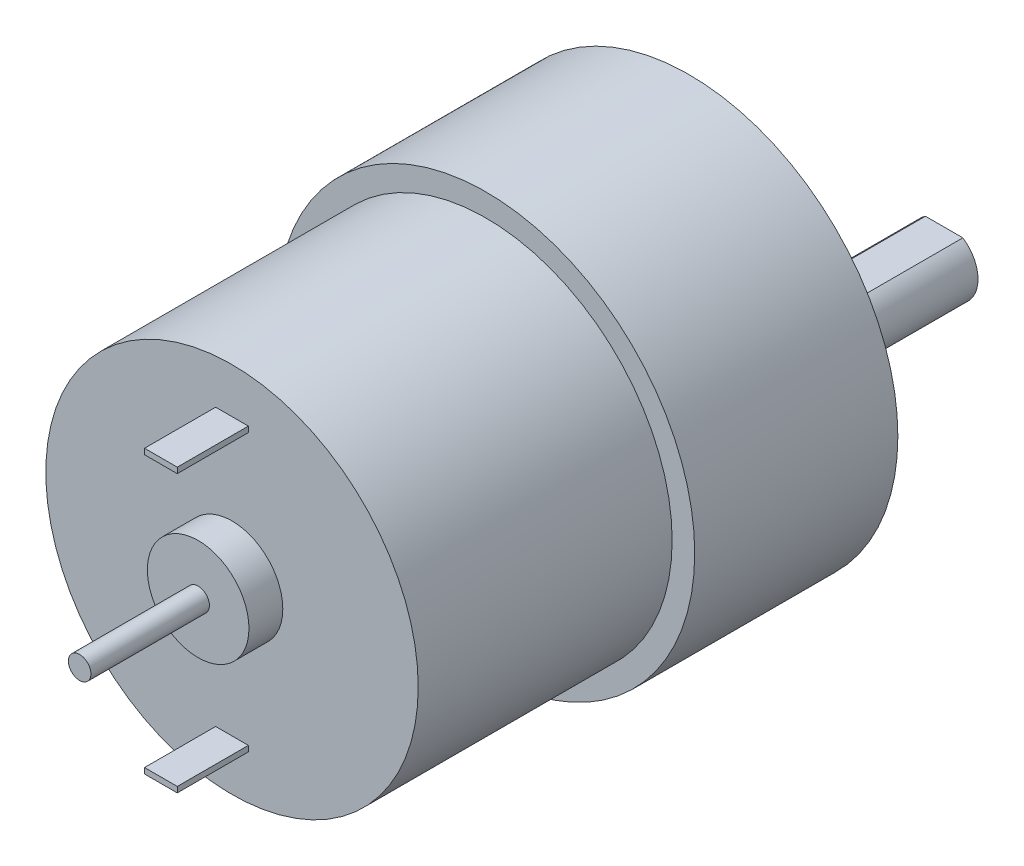
SolidWorks part; units mm, degrees
ref_plane "Alzado" through (0, 0, 0) normal (0, 0, 1) x (1, 0, 0)
ref_plane "Planta" through (0, 0, 0) normal (0, 1, 0) x (1, 0, 0)
ref_plane "Vista lateral" through (0, 0, 0) normal (1, 0, 0) x (0, 0, -1)
sketch "Croquis1" plane through (0, 0, 0) normal (0, 0, 1) x (1, 0, 0)
  circle A0 centre (0, 0) radius 18.5
  dimension "D1" = 37
extrude "Saliente-Extruir1" add sketch "Croquis1" along normal blind 18
sketch "Croquis2" plane through (0, 0, 18) normal (0, 0, 1) x (1, 0, 0)
  circle A0 centre (0, 0) radius 16.5
  dimension "D1" = 33
extrude "Saliente-Extruir2" add sketch "Croquis2" along normal blind 22.5
sketch "Croquis3" plane through (0, 0, 40.5) normal (0, 0, 1) x (1, 0, 0)
  circle A0 centre (0, 0) radius 4.5
  dimension "D1" = 9
extrude "Saliente-Extruir3" add sketch "Croquis3" along normal blind 3
sketch "Croquis4" plane through (0, 0, 43.5) normal (0, 0, 1) x (1, 0, 0)
  circle A0 centre (0, 0) radius 1
  dimension "D1" = 2
extrude "Saliente-Extruir4" add sketch "Croquis4" along normal blind 10.5
sketch "Croquis5" plane through (0, 0, 40.5) normal (0, 0, 1) x (1, 0, 0)
  line L0 (0, 16.5) -> (0, 12.25) construction
  line L1 (0, 12.25) -> (0, -12.25) construction
  line L2 (0, -12.25) -> (0, -16.5) construction
  line L4 (1.45, 12.5) -> (-1.45, 12.5)
  line L5 (1.45, 12.5) -> (1.45, 12)
  line L6 (1.45, 12) -> (-1.45, 12)
  line L7 (-1.45, 12.5) -> (-1.45, 12)
  line L8 (1.45, 12.5) -> (-1.45, 12) construction
  line L9 (1.45, 12) -> (-1.45, 12.5) construction
  line L10 (1.45, -12.5) -> (-1.45, -12.5)
  line L11 (1.45, -12.5) -> (1.45, -12)
  line L12 (1.45, -12) -> (-1.45, -12)
  line L13 (-1.45, -12.5) -> (-1.45, -12)
  line L14 (1.45, -12.5) -> (-1.45, -12) construction
  line L15 (1.45, -12) -> (-1.45, -12.5) construction
  circle A1 centre (0, 0) radius 16.5 construction
  dimension "D1" = 0.5
  dimension "D2" = 2.9
  dimension "D3" = 25
extrude "Saliente-Extruir5" add sketch "Croquis5" along normal blind 6.3
sketch "Croquis6" plane through (0, 0, 0) normal (0, 0, -1) x (-1, 0, 0)
  line L0 (0, 0) -> (0, -7) construction
  circle A0 centre (0, -7) radius 6
  dimension "D2" = 12
  dimension "D1" = 7
extrude "Saliente-Extruir6" add sketch "Croquis6" along normal blind 4.6
sketch "Croquis7" plane through (0, 0, -4.6) normal (0, 0, -1) x (-1, 0, 0)
  circle A0 centre (0, -7) radius 3
  dimension "D1" = 6
extrude "Saliente-Extruir7" add sketch "Croquis7" along normal blind 6
sketch "Croquis8" plane through (0, 0, -10.6) normal (0, 0, -1) x (-1, 0, 0)
  line L0 (-1.6583, -4.5) -> (1.6583, -4.5)
  circle A0 centre (0, -7) radius 3 construction
  arc A1 (1.6583, -4.5) -> (-1.6583, -4.5) centre (0, -7) cw
  point P5 (0, -10)
  dimension "D1" = 5.5
extrude "Saliente-Extruir8" add sketch "Croquis8" along normal blind 12
sketch "Croquis9" plane through (0, 0, 0) normal (0, 0, -1) x (-1, 0, 0)
  line L0 (0, 0) -> (15.5, 0) construction
  line L1 (0, 0) -> (-15.5, 0) construction
  line L2 (-7.75, 13.4234) -> (0, 0) construction
  line L3 (0, 0) -> (-7.75, -13.4234) construction
  circle A0 centre (0, 0) radius 15.5 construction
  circle A1 centre (-7.75, 13.4234) radius 1.5
  circle A2 centre (-15.5, 0) radius 1.5
  circle A3 centre (-7.75, -13.4234) radius 1.5
  circle A4 centre (15.5, 0) radius 1.5
  dimension "D3" = 31
  dimension "D4" = 3
  dimension "D1" = 120
  dimension "D2" = 120
extrude "Cortar-Extruir1" cut sketch "Croquis9" against normal blind 5
